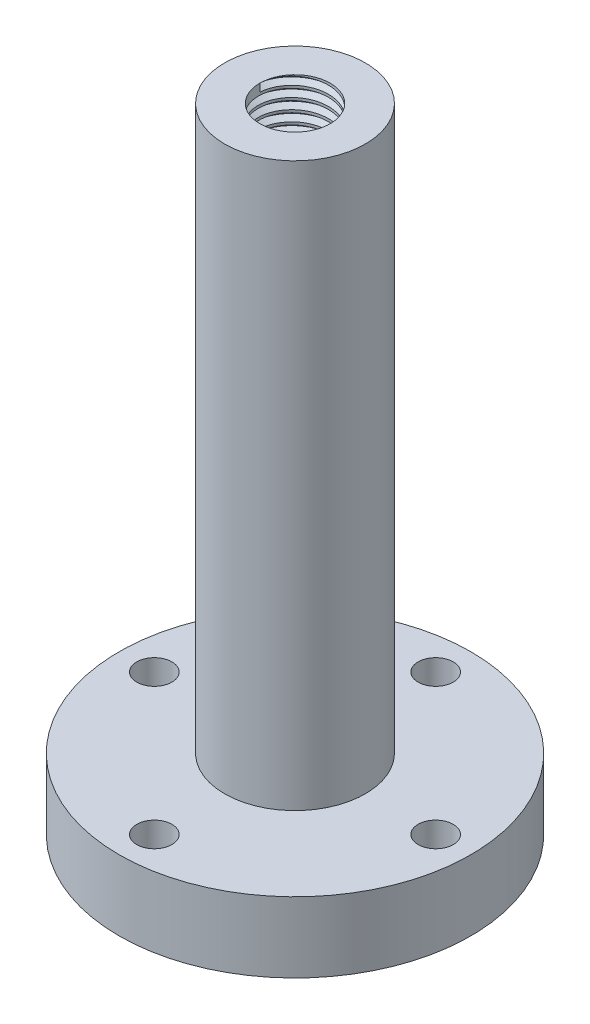
SolidWorks part; units mm, degrees
ref_plane "Front Plane" through (0, 0, 0) normal (0, 0, 1) x (1, 0, 0)
ref_plane "Top Plane" through (0, 0, 0) normal (0, 1, 0) x (1, 0, 0)
ref_plane "Right Plane" through (0, 0, 0) normal (1, 0, 0) x (0, 0, -1)
sketch "Sketch1" plane through (0, 0, 0) normal (0, 1, 0) x (1, 0, 0)
  circle A0 centre (0, 0) radius 25
extrude "Boss-Extrude1" add sketch "Sketch1" along normal blind 10
sketch "Sketch2" plane through (0, 10, 0) normal (0, 1, 0) x (1, 0, 0)
  circle A0 centre (0, 0) radius 10
extrude "Boss-Extrude2" add sketch "Sketch2" along normal blind 80
sketch "Sketch3" plane through (0, 90, 0) normal (0, 1, 0) x (1, 0, 0)
  circle A0 centre (0, 0) radius 5
extrude "Cut-Extrude1" cut sketch "Sketch3" against normal through all
thread "Thread1" pitch 1.5 profile "Thread Profile1" start angle 0, offset 0, length 10, pitch 1.5, diameter 10
ref_plane "Plane1" through (-5, 90, 0) normal (0, 0, 1) x (-1, 0, 0)
sketch "Thread Profile1" plane through (-5, 90, 0) normal (0, 0, 1) x (-1, 0, 0)
  line L0 (0, 0) -> (0, 1.5) construction
  line L1 (0, 0) -> (0.8119, 0.4687)
  line L2 (0.8119, 0.4687) -> (0.8119, 0.6562)
  line L3 (0.8119, 0.6562) -> (0, 1.125)
  line L4 (0.8119, 0.5625) -> (0, 0.5625) construction
  line L11 (0, 0) -> (0, 1.125)
  point P2 (0, 0)
  dimension "Pitch" = 1.5
  dimension "Profile_Angle" = 60
  dimension "Profile_Land" = 0.1875
  dimension "Profile_Height" = 0.8119
sketch "Sketch6" plane through (0, 0, 0) normal (0, -1, 0) x (1, 0, 0)
  circle A0 centre (0, 20) radius 2.5
  circle A1 centre (20, 0) radius 2.5
  circle A2 centre (0, -20) radius 2.5
  circle A3 centre (-20, 0) radius 2.5
  point P12 (0, 0)
  dimension "D1" = 20
  dimension "D2" = 4
extrude "Cut-Extrude2" cut sketch "Sketch6" against normal through all
